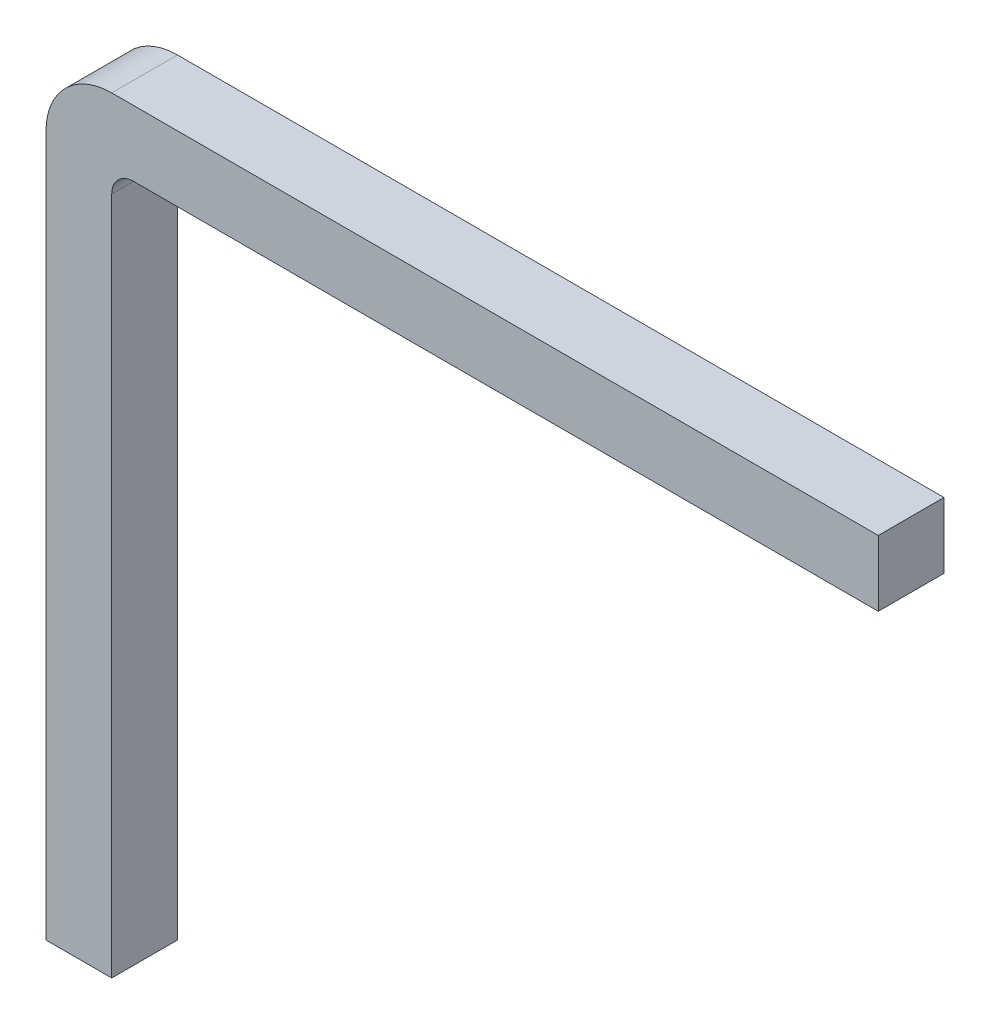
SolidWorks part; units mm, degrees
ref_plane "Front Plane" through (0, 0, 0) normal (0, 0, 1) x (1, 0, 0)
ref_plane "Top Plane" through (0, 0, 0) normal (0, 1, 0) x (1, 0, 0)
ref_plane "Right Plane" through (0, 0, 0) normal (1, 0, 0) x (0, 0, -1)
sketch "Sketch3" plane through (0, 0, 0) normal (0, 0, 1) x (1, 0, 0)
  line L0 (0, 0) -> (0, 6.7) construction
  line L2 (0, 6.7) -> (7.3, 6.7) construction
  line L3 (0, 0) -> (-0.3, 0)
  line L4 (-0.3, 0) -> (-0.3, 6.4)
  line L5 (0.3, 7) -> (7.3, 7)
  line L6 (7.3, 7) -> (7.3, 6.4)
  line L7 (7.3, 6.4) -> (0.5, 6.4)
  line L8 (0.3, 6.2) -> (0.3, 0)
  line L9 (0.3, 0) -> (0, 0)
  arc A0 (-0.3, 6.4) -> (0.3, 7) centre (0.3, 6.4) cw
  arc A1 (0.3, 6.2) -> (0.5, 6.4) centre (0.5, 6.2) cw
  dimension "D5" = 0.6
  dimension "D6" = 0.2
  dimension "D1" = 0.6
  dimension "D2" = 0.6
  dimension "D3" = 7
  dimension "D4" = 7.6
extrude "Boss-Extrude1" add sketch "Sketch3" along normal mid plane 0.6
